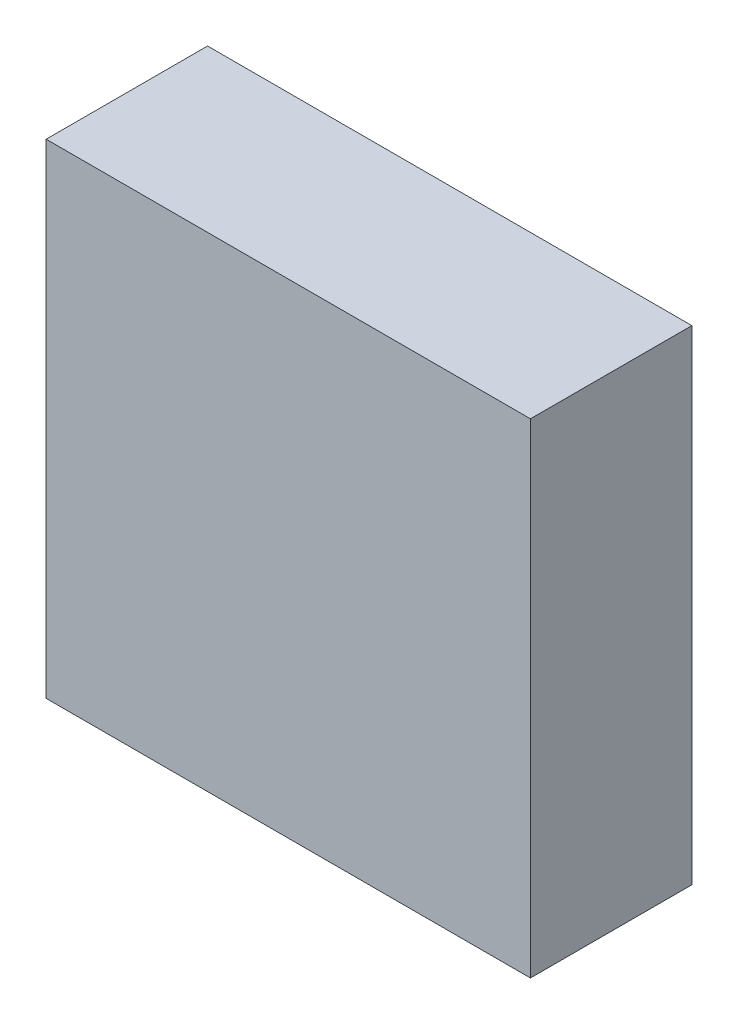
SolidWorks part; units mm, degrees
ref_plane "Front Plane" through (0, 0, 0) normal (0, 0, 1) x (1, 0, 0)
ref_plane "Top Plane" through (0, 0, 0) normal (0, 1, 0) x (1, 0, 0)
ref_plane "Right Plane" through (0, 0, 0) normal (1, 0, 0) x (0, 0, -1)
sketch "Sketch1" plane through (0, 0, 0) normal (0, 0, 1) x (1, 0, 0)
  line L1 (-15, -15) -> (15, -15)
  line L2 (-15, -15) -> (-15, 15)
  line L3 (-15, 15) -> (15, 15)
  line L4 (15, -15) -> (15, 15)
  line L5 (-15, -15) -> (15, 15) construction
  line L6 (-15, 15) -> (15, -15) construction
  point P1 (0, 0)
  dimension "D1" = 30
  dimension "D2" = 30
extrude "Boss-Extrude1" add sketch "Sketch1" along normal blind 10
